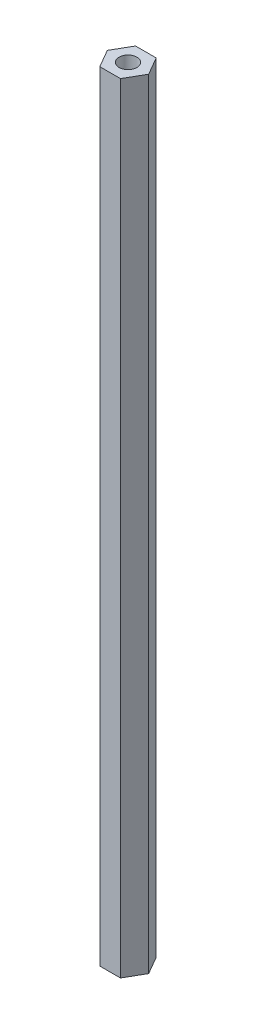
SolidWorks part; units mm, degrees
ref_plane "Front Plane" through (0, 0, 0) normal (0, 0, 1) x (1, 0, 0)
ref_plane "Top Plane" through (0, 0, 0) normal (0, 1, 0) x (1, 0, 0)
ref_plane "Right Plane" through (0, 0, 0) normal (1, 0, 0) x (0, 0, -1)
sketch "Sketch1" plane through (0, 0, 0) normal (0, 1, 0) x (1, 0, 0)
  line L1 (-2.0207, 3.5) -> (-4.0415, 0)
  line L2 (-4.0415, 0) -> (-2.0207, -3.5)
  line L3 (-2.0207, -3.5) -> (2.0207, -3.5)
  line L4 (2.0207, -3.5) -> (4.0415, 0)
  line L5 (4.0415, 0) -> (2.0207, 3.5)
  line L6 (2.0207, 3.5) -> (-2.0207, 3.5)
  circle A0 centre (0, 0) radius 3.5 construction
  dimension "D1" = 7
extrude "Boss-Extrude1" add sketch "Sketch1" along normal blind 152.4
sketch "Sketch2" plane through (0, 152.4, 0) normal (0, 1, 0) x (1, 0, 0)
  circle A0 centre (0, 0) radius 1.75
  dimension "D1" = 3.5
extrude "Cut-Extrude1" cut sketch "Sketch2" against normal blind 2000
